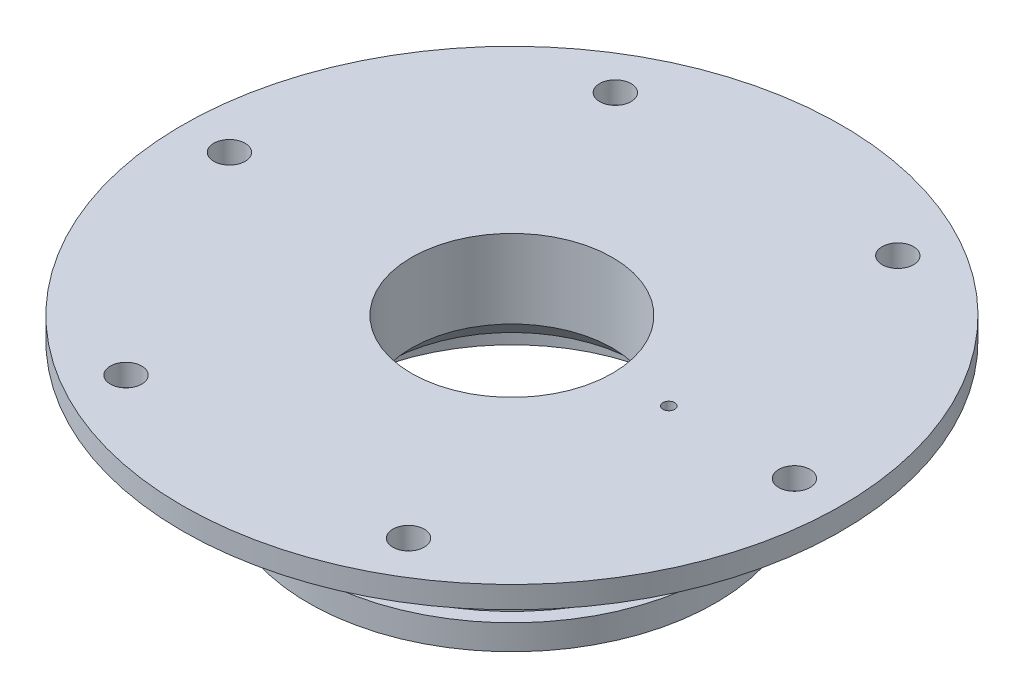
SolidWorks part; units mm, degrees
material "6061-T6 (SS)"
ref_plane "Front Plane" through (0, 0, 0) normal (0, 0, 1) x (1, 0, 0)
ref_plane "Top Plane" through (0, 0, 0) normal (0, 1, 0) x (1, 0, 0)
ref_plane "Right Plane" through (0, 0, 0) normal (1, 0, 0) x (0, 0, -1)
ref_axis "Axis1" through (0, -0.4763, 0) along (0, 1, 0)
ref_plane "Plane2" through (0, 0, 0) normal (0.5, 0, 0.866) x (0, 1, 0)
sketch "Sketch1" plane through (0, 0, 0) normal (0, 1, 0) x (1, 0, 0)
  circle A0 centre (0, 0) radius 66.675
  circle A1 centre (0, 0) radius 20.32
  dimension "D1" = 133.35
  dimension "D2" = 40.64
extrude "Boss-Extrude1" add sketch "Sketch1" along normal blind 4.445
sketch "Sketch2" plane through (0, 0, 0) normal (0, 0, 1) x (1, 0, 0)
  line L1 (41.275, 0) -> (44.45, 0)
  line L2 (41.275, 0) -> (41.275, 3.81)
  line L3 (41.275, 3.81) -> (44.45, 3.81)
  line L4 (44.45, 0) -> (44.45, 3.81)
  line L6 (73.3425, 0) -> (-73.3425, 0) construction
  dimension "D1" = 3.81
  dimension "D2" = 3.175
  dimension "D3" = 44.45
revolve "Cut-Revolve1" [suppressed] cut sketch "Sketch2" angle 360 about axis through (0, -0.4763, 0) along (0, 1, 0)
hole_wizard "1/4 (0.25) Diameter Hole1" positions "Sketch5" profile "Sketch4" hole size "1/4" standard "ANSI Inch" end condition up to next
sketch "Sketch5" plane through (0, 4.445, 0) normal (0, 1, 0) x (1, 0, 0)
  line L0 (-55, 0) -> (55, 0) construction
  point P0 (57.15, 0)
  dimension "D1" = 57.15
sketch "Sketch4" plane through (57.15, 4.445, 0) normal (1, 0, 0) x (0, 0, 1)
  line L0 (0, 0) -> (0, 4.446)
  line L1 (0, 4.446) -> (3.175, 4.446)
  line L2 (3.175, 4.446) -> (3.175, 0)
  line L5 (3.175, 0) -> (0, 0)
  line L11 (0, -6.35) -> (0, 107.95) construction
  dimension "Thru Hole Dia." = 6.35
  dimension "Thru Hole Depth" = 4.446
pattern_circular "CirPattern1" count 6 over 360 about axis through (0, 0, 0) along (0, 1, 0) of "1/4 (0.25) Diameter Hole1"
sketch "Sketch6" plane through (0, 0, 0) normal (0, -1, 0) x (1, 0, 0)
  circle A0 centre (0, 0) radius 20.32
  circle A1 centre (0, 0) radius 41.148
  dimension "D1" = 82.296
  dimension "D2" = 40.64
extrude "Boss-Extrude2" add sketch "Sketch6" along normal blind 25.4
ref_plane "Plane1" through (0, -25.4, 0) normal (-1, 0, 0) x (0, 0, 1)
sketch "Sketch9" plane through (0, 0, 0) normal (0, 0, 1) x (1, 0, 0)
  line L0 (0, -0.4763) -> (0, 10.0012) construction
  line L1 (41.275, -20.32) -> (38.3413, -20.32)
  line L2 (41.275, -20.32) -> (41.275, -15.24)
  line L3 (41.275, -15.24) -> (38.3413, -15.24)
  line L4 (38.3413, -20.32) -> (38.3413, -15.24)
  line L8 (-41.148, -25.4) -> (41.148, -25.4) construction
  dimension "D1" = 38.3413
  dimension "D2" = 5.08
  dimension "D3" = 41.275
  dimension "D4" = 5.08
revolve "Cut-Revolve3" cut sketch "Sketch9" angle 360 about axis through (0, -0.4763, 0) along (0, 1, 0)
pattern_linear "LPattern1" [suppressed] count 2 spacing 10.16
hole_wizard "1/4-20 Tapped Hole1" positions "3DSketch1" profile "Sketch10" tap size "1/4-20" standard "ANSI Inch"
sketch3d "3DSketch1"
  point P0 (-35.6352, -7.62, 20.574)
  dimension "D1" = 7.62
cosmetic thread "Hole Thread1" parameters "D1"=8.89, "D2"=6.35
sketch "Sketch10" plane through (-35.6352, -7.62, 20.574) normal (0, 1, 0) x (0.5, 0, 0.866)
  line L0 (0, 0) -> (0, 14.2338)
  line L1 (0, 14.2338) -> (2.5527, 12.7)
  line L2 (2.5527, 12.7) -> (2.5527, 0)
  line L5 (2.5527, 0) -> (0, 0)
  line L10 (0, 14.2338) -> (-2.5527, 12.7) construction
  line L11 (0, -6.35) -> (0, 107.95) construction
  dimension "Tap Drill Dia." = 5.1054
  dimension "Tap Drill Depth" = 12.7
  dimension "Drill Angle" = 118
pattern_circular "CirPattern2" count 6 over 360 about axis through (0, -0.4763, 0) along (0, 1, 0) of "1/4-20 Tapped Hole1"
hole_wizard "3/32 (0.09375) Diameter Hole1" positions "Sketch11" profile "Sketch12" hole size "3/32" standard "ANSI Inch" end condition through all
sketch "Sketch11" plane through (0, 4.445, 0) normal (0, 1, 0) x (1, 0, 0)
  line L1 (-55, 0) -> (55, 0) construction
  point P0 (31.75, 0)
  dimension "D1" = 31.75
sketch "Sketch12" plane through (31.75, 4.445, 0) normal (1, 0, 0) x (0, 0, 1)
  line L0 (0, 0) -> (0, 29.845)
  line L1 (0, 29.845) -> (1.1906, 29.845)
  line L2 (1.1906, 29.845) -> (1.1906, 0)
  line L5 (1.1906, 0) -> (0, 0)
  line L11 (0, -6.35) -> (0, 107.95) construction
  dimension "Thru Hole Dia." = 2.3812
  dimension "Thru Hole Depth" = 29.845
sketch "Sketch13" plane through (0, -25.4, 0) normal (0, -1, 0) x (1, 0, 0)
  circle A0 centre (0, 0) radius 34.925
  dimension "D1" = 69.85
extrude "Cut-Extrude1" cut sketch "Sketch13" against normal blind 8.89
chamfer "Chamfer1" [suppressed] distance 6.35 angle 60
chamfer "Chamfer2" distance 5.08 angle 45 1 edges at (0, -16.51, -20.32)
